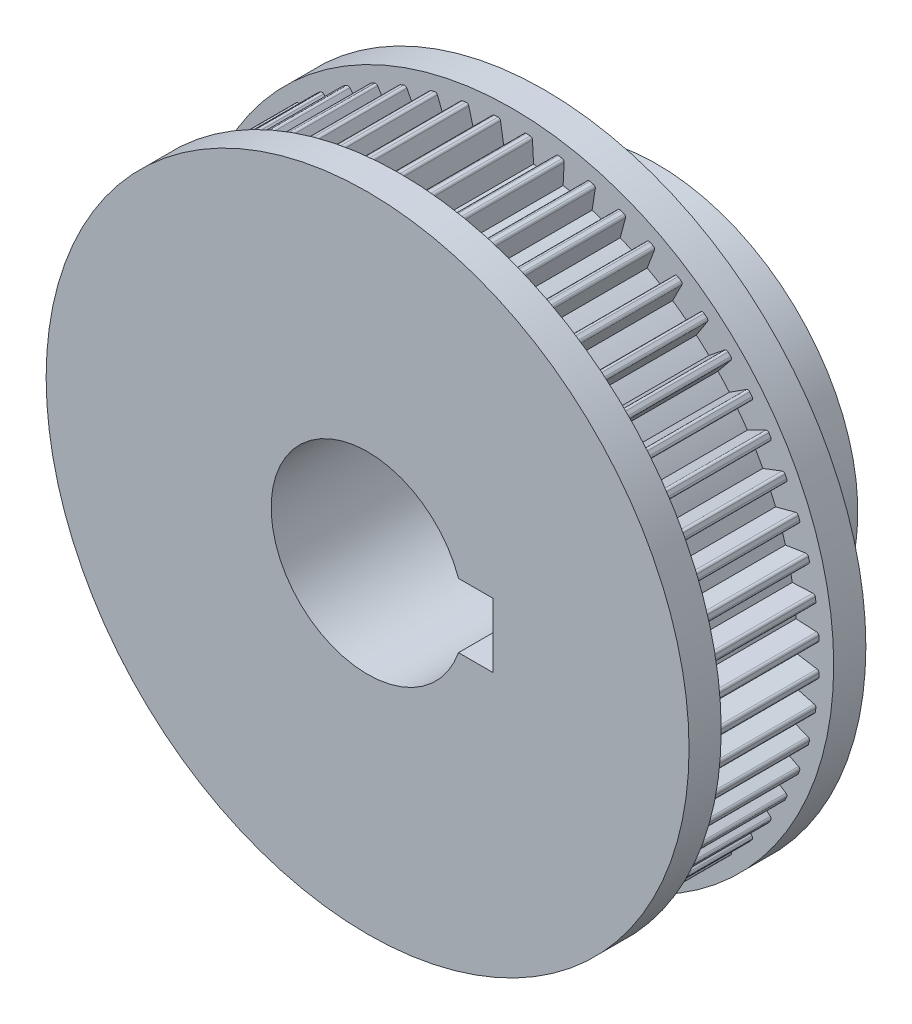
SolidWorks part; units mm, degrees
ref_plane "Front Plane" through (0, 0, 0) normal (0, 0, 1) x (1, 0, 0)
ref_plane "Top Plane" through (0, 0, 0) normal (0, 1, 0) x (1, 0, 0)
ref_plane "Right Plane" through (0, 0, 0) normal (1, 0, 0) x (0, 0, -1)
sketch "Sketch1" plane through (0, 0, 0) normal (0, 0, 1) x (1, 0, 0)
  line L0 (0, 0) -> (0, 9.7797) construction
  line L1 (0, 0) -> (0.9553, 9.0894) construction
  line L2 (-0.7503, 19.0926) -> (-0.527, 17.6995)
  line L3 (1.2496, 19.0664) -> (1.3259, 17.6576) construction
  line L4 (0.7503, 19.0926) -> (0.527, 17.6995)
  line L5 (2.7419, 18.9096) -> (2.3743, 17.5474) construction
  line L6 (1.2496, 19.0664) -> (1.3259, 17.6576)
  line L7 (2.7419, 18.9096) -> (2.3743, 17.5474)
  line L8 (3.2357, 18.8314) -> (3.1644, 17.4223)
  line L9 (4.7034, 18.5194) -> (4.1955, 17.2031)
  line L10 (5.1864, 18.39) -> (4.9682, 16.9961)
  line L11 (6.6135, 17.9263) -> (5.9707, 16.6703)
  line L12 (7.0803, 17.7471) -> (6.7175, 16.3836)
  line L13 (8.451, 17.1368) -> (7.6805, 15.9549)
  line L14 (8.8966, 16.9098) -> (8.3933, 15.5917)
  line L15 (10.196, 16.1595) -> (9.3062, 15.0647)
  line L16 (10.6154, 15.8872) -> (9.9771, 14.629)
  line L17 (11.8293, 15.0052) -> (10.8299, 14.0094)
  line L18 (12.2179, 14.6906) -> (11.4516, 13.5059)
  line L19 (13.333, 13.6865) -> (12.2349, 12.8006)
  line L20 (13.6865, 13.333) -> (12.8006, 12.2349)
  line L21 (14.6906, 12.2179) -> (13.5059, 11.4516)
  line L22 (15.0052, 11.8293) -> (14.0094, 10.8299)
  line L23 (15.8872, 10.6154) -> (14.629, 9.9771)
  line L24 (16.1595, 10.196) -> (15.0647, 9.3062)
  line L25 (16.9098, 8.8966) -> (15.5917, 8.3933)
  line L26 (17.1368, 8.451) -> (15.9549, 7.6805)
  line L27 (17.7471, 7.0803) -> (16.3836, 6.7175)
  line L28 (17.9263, 6.6135) -> (16.6703, 5.9707)
  line L29 (18.39, 5.1864) -> (16.9961, 4.9682)
  line L30 (18.5194, 4.7034) -> (17.2031, 4.1955)
  line L31 (18.8314, 3.2357) -> (17.4223, 3.1644)
  line L32 (18.9096, 2.7419) -> (17.5474, 2.3743)
  line L33 (19.0664, 1.2496) -> (17.6576, 1.3259)
  line L34 (19.0926, 0.7503) -> (17.6995, 0.527)
  line L35 (19.0926, -0.7503) -> (17.6995, -0.527)
  line L36 (19.0664, -1.2496) -> (17.6576, -1.3259)
  line L37 (18.9096, -2.7419) -> (17.5474, -2.3743)
  line L38 (18.8314, -3.2357) -> (17.4223, -3.1644)
  line L39 (18.5194, -4.7034) -> (17.2031, -4.1955)
  line L40 (18.39, -5.1864) -> (16.9961, -4.9682)
  line L41 (17.9263, -6.6135) -> (16.6703, -5.9707)
  line L42 (17.7471, -7.0803) -> (16.3836, -6.7175)
  line L43 (17.1368, -8.451) -> (15.9549, -7.6805)
  line L44 (16.9098, -8.8966) -> (15.5917, -8.3933)
  line L45 (16.1595, -10.196) -> (15.0647, -9.3062)
  line L46 (15.8872, -10.6154) -> (14.629, -9.9771)
  line L47 (15.0052, -11.8293) -> (14.0094, -10.8299)
  line L48 (14.6906, -12.2179) -> (13.5059, -11.4516)
  line L49 (13.6865, -13.333) -> (12.8006, -12.2349)
  line L50 (13.333, -13.6865) -> (12.2349, -12.8006)
  line L51 (12.2179, -14.6906) -> (11.4516, -13.5059)
  line L52 (11.8293, -15.0052) -> (10.8299, -14.0094)
  line L53 (10.6154, -15.8872) -> (9.9771, -14.629)
  line L54 (10.196, -16.1595) -> (9.3062, -15.0647)
  line L55 (8.8966, -16.9098) -> (8.3933, -15.5917)
  line L56 (8.451, -17.1368) -> (7.6805, -15.9549)
  line L57 (7.0803, -17.7471) -> (6.7175, -16.3836)
  line L58 (6.6135, -17.9263) -> (5.9707, -16.6703)
  line L59 (5.1864, -18.39) -> (4.9682, -16.9961)
  line L60 (4.7034, -18.5194) -> (4.1955, -17.2031)
  line L61 (3.2357, -18.8314) -> (3.1644, -17.4223)
  line L62 (2.7419, -18.9096) -> (2.3743, -17.5474)
  line L63 (1.2496, -19.0664) -> (1.3259, -17.6576)
  line L64 (0.7503, -19.0926) -> (0.527, -17.6995)
  line L65 (-0.7503, -19.0926) -> (-0.527, -17.6995)
  line L66 (-1.2496, -19.0664) -> (-1.3259, -17.6576)
  line L67 (-2.7419, -18.9096) -> (-2.3743, -17.5474)
  line L68 (-3.2357, -18.8314) -> (-3.1644, -17.4223)
  line L69 (-4.7034, -18.5194) -> (-4.1955, -17.2031)
  line L70 (-5.1864, -18.39) -> (-4.9682, -16.9961)
  line L71 (-6.6135, -17.9263) -> (-5.9707, -16.6703)
  line L72 (-7.0803, -17.7471) -> (-6.7175, -16.3836)
  line L73 (-8.451, -17.1368) -> (-7.6805, -15.9549)
  line L74 (-8.8966, -16.9098) -> (-8.3933, -15.5917)
  line L75 (-10.196, -16.1595) -> (-9.3062, -15.0647)
  line L76 (-10.6154, -15.8872) -> (-9.9771, -14.629)
  line L77 (-11.8293, -15.0052) -> (-10.8299, -14.0094)
  line L78 (-12.2179, -14.6906) -> (-11.4516, -13.5059)
  line L79 (-13.333, -13.6865) -> (-12.2349, -12.8006)
  line L80 (-13.6865, -13.333) -> (-12.8006, -12.2349)
  line L81 (-14.6906, -12.2179) -> (-13.5059, -11.4516)
  line L82 (-15.0052, -11.8293) -> (-14.0094, -10.8299)
  line L83 (-15.8872, -10.6154) -> (-14.629, -9.9771)
  line L84 (-16.1595, -10.196) -> (-15.0647, -9.3062)
  line L85 (-16.9098, -8.8966) -> (-15.5917, -8.3933)
  line L86 (-17.1368, -8.451) -> (-15.9549, -7.6805)
  line L87 (-17.7471, -7.0803) -> (-16.3836, -6.7175)
  line L88 (-17.9263, -6.6135) -> (-16.6703, -5.9707)
  line L89 (-18.39, -5.1864) -> (-16.9961, -4.9682)
  line L90 (-18.5194, -4.7034) -> (-17.2031, -4.1955)
  line L91 (-18.8314, -3.2357) -> (-17.4223, -3.1644)
  line L92 (-18.9096, -2.7419) -> (-17.5474, -2.3743)
  line L93 (-19.0664, -1.2496) -> (-17.6576, -1.3259)
  line L94 (-19.0926, -0.7503) -> (-17.6995, -0.527)
  line L95 (-19.0926, 0.7503) -> (-17.6995, 0.527)
  line L96 (-19.0664, 1.2496) -> (-17.6576, 1.3259)
  line L97 (-18.9096, 2.7419) -> (-17.5474, 2.3743)
  line L98 (-18.8314, 3.2357) -> (-17.4223, 3.1644)
  line L99 (-18.5194, 4.7034) -> (-17.2031, 4.1955)
  line L100 (-18.39, 5.1864) -> (-16.9961, 4.9682)
  line L101 (-17.9263, 6.6135) -> (-16.6703, 5.9707)
  line L102 (-17.7471, 7.0803) -> (-16.3836, 6.7175)
  line L103 (-17.1368, 8.451) -> (-15.9549, 7.6805)
  line L104 (-16.9098, 8.8966) -> (-15.5917, 8.3933)
  line L105 (-16.1595, 10.196) -> (-15.0647, 9.3062)
  line L106 (-15.8872, 10.6154) -> (-14.629, 9.9771)
  line L107 (-15.0052, 11.8293) -> (-14.0094, 10.8299)
  line L108 (-14.6906, 12.2179) -> (-13.5059, 11.4516)
  line L109 (-13.6865, 13.333) -> (-12.8006, 12.2349)
  line L110 (-13.333, 13.6865) -> (-12.2349, 12.8006)
  line L111 (-12.2179, 14.6906) -> (-11.4516, 13.5059)
  line L112 (-11.8293, 15.0052) -> (-10.8299, 14.0094)
  line L113 (-10.6154, 15.8872) -> (-9.9771, 14.629)
  line L114 (-10.196, 16.1595) -> (-9.3062, 15.0647)
  line L115 (-8.8966, 16.9098) -> (-8.3933, 15.5917)
  line L116 (-8.451, 17.1368) -> (-7.6805, 15.9549)
  line L117 (-7.0803, 17.7471) -> (-6.7175, 16.3836)
  line L118 (-6.6135, 17.9263) -> (-5.9707, 16.6703)
  line L119 (-5.1864, 18.39) -> (-4.9682, 16.9961)
  line L120 (-4.7034, 18.5194) -> (-4.1955, 17.2031)
  line L121 (-3.2357, 18.8314) -> (-3.1644, 17.4223)
  line L122 (-2.7419, 18.9096) -> (-2.3743, 17.5474)
  line L123 (-1.2496, 19.0664) -> (-1.3259, 17.6576)
  arc A0 (2.3743, 17.5474) -> (1.3259, 17.6576) centre (0, 0) ccw construction
  arc A1 (2.7419, 18.9096) -> (1.2496, 19.0664) centre (0, 0) ccw construction
  arc A2 (0.527, 17.6995) -> (-0.527, 17.6995) centre (0, 0) ccw
  arc A3 (0.7503, 19.0926) -> (-0.7503, 19.0926) centre (0, 0) ccw
  arc A4 (2.7419, 18.9096) -> (1.2496, 19.0664) centre (0, 0) ccw
  arc A5 (2.3743, 17.5474) -> (1.3259, 17.6576) centre (0, 0) ccw
  arc A6 (4.7034, 18.5194) -> (3.2357, 18.8314) centre (0, 0) ccw
  arc A7 (4.1955, 17.2031) -> (3.1644, 17.4223) centre (0, 0) ccw
  arc A8 (6.6135, 17.9263) -> (5.1864, 18.39) centre (0, 0) ccw
  arc A9 (5.9707, 16.6703) -> (4.9682, 16.9961) centre (0, 0) ccw
  arc A10 (8.451, 17.1368) -> (7.0803, 17.7471) centre (0, 0) ccw
  arc A11 (7.6805, 15.9549) -> (6.7175, 16.3836) centre (0, 0) ccw
  arc A12 (10.196, 16.1595) -> (8.8966, 16.9098) centre (0, 0) ccw
  arc A13 (9.3062, 15.0647) -> (8.3933, 15.5917) centre (0, 0) ccw
  arc A14 (11.8293, 15.0052) -> (10.6154, 15.8872) centre (0, 0) ccw
  arc A15 (10.8299, 14.0094) -> (9.9771, 14.629) centre (0, 0) ccw
  arc A16 (13.333, 13.6865) -> (12.2179, 14.6906) centre (0, 0) ccw
  arc A17 (12.2349, 12.8006) -> (11.4516, 13.5059) centre (0, 0) ccw
  arc A18 (14.6906, 12.2179) -> (13.6865, 13.333) centre (0, 0) ccw
  arc A19 (13.5059, 11.4516) -> (12.8006, 12.2349) centre (0, 0) ccw
  arc A20 (15.8872, 10.6154) -> (15.0052, 11.8293) centre (0, 0) ccw
  arc A21 (14.629, 9.9771) -> (14.0094, 10.8299) centre (0, 0) ccw
  arc A22 (16.9098, 8.8966) -> (16.1595, 10.196) centre (0, 0) ccw
  arc A23 (15.5917, 8.3933) -> (15.0647, 9.3062) centre (0, 0) ccw
  arc A24 (17.7471, 7.0803) -> (17.1368, 8.451) centre (0, 0) ccw
  arc A25 (16.3836, 6.7175) -> (15.9549, 7.6805) centre (0, 0) ccw
  arc A26 (18.39, 5.1864) -> (17.9263, 6.6135) centre (0, 0) ccw
  arc A27 (16.9961, 4.9682) -> (16.6703, 5.9707) centre (0, 0) ccw
  arc A28 (18.8314, 3.2357) -> (18.5194, 4.7034) centre (0, 0) ccw
  arc A29 (17.4223, 3.1644) -> (17.2031, 4.1955) centre (0, 0) ccw
  arc A30 (19.0664, 1.2496) -> (18.9096, 2.7419) centre (0, 0) ccw
  arc A31 (17.6576, 1.3259) -> (17.5474, 2.3743) centre (0, 0) ccw
  arc A32 (19.0926, -0.7503) -> (19.0926, 0.7503) centre (0, 0) ccw
  arc A33 (17.6995, -0.527) -> (17.6995, 0.527) centre (0, 0) ccw
  arc A34 (18.9096, -2.7419) -> (19.0664, -1.2496) centre (0, 0) ccw
  arc A35 (17.5474, -2.3743) -> (17.6576, -1.3259) centre (0, 0) ccw
  arc A36 (18.5194, -4.7034) -> (18.8314, -3.2357) centre (0, 0) ccw
  arc A37 (17.2031, -4.1955) -> (17.4223, -3.1644) centre (0, 0) ccw
  arc A38 (17.9263, -6.6135) -> (18.39, -5.1864) centre (0, 0) ccw
  arc A39 (16.6703, -5.9707) -> (16.9961, -4.9682) centre (0, 0) ccw
  arc A40 (17.1368, -8.451) -> (17.7471, -7.0803) centre (0, 0) ccw
  arc A41 (15.9549, -7.6805) -> (16.3836, -6.7175) centre (0, 0) ccw
  arc A42 (16.1595, -10.196) -> (16.9098, -8.8966) centre (0, 0) ccw
  arc A43 (15.0647, -9.3062) -> (15.5917, -8.3933) centre (0, 0) ccw
  arc A44 (15.0052, -11.8293) -> (15.8872, -10.6154) centre (0, 0) ccw
  arc A45 (14.0094, -10.8299) -> (14.629, -9.9771) centre (0, 0) ccw
  arc A46 (13.6865, -13.333) -> (14.6906, -12.2179) centre (0, 0) ccw
  arc A47 (12.8006, -12.2349) -> (13.5059, -11.4516) centre (0, 0) ccw
  arc A48 (12.2179, -14.6906) -> (13.333, -13.6865) centre (0, 0) ccw
  arc A49 (11.4516, -13.5059) -> (12.2349, -12.8006) centre (0, 0) ccw
  arc A50 (10.6154, -15.8872) -> (11.8293, -15.0052) centre (0, 0) ccw
  arc A51 (9.9771, -14.629) -> (10.8299, -14.0094) centre (0, 0) ccw
  arc A52 (8.8966, -16.9098) -> (10.196, -16.1595) centre (0, 0) ccw
  arc A53 (8.3933, -15.5917) -> (9.3062, -15.0647) centre (0, 0) ccw
  arc A54 (7.0803, -17.7471) -> (8.451, -17.1368) centre (0, 0) ccw
  arc A55 (6.7175, -16.3836) -> (7.6805, -15.9549) centre (0, 0) ccw
  arc A56 (5.1864, -18.39) -> (6.6135, -17.9263) centre (0, 0) ccw
  arc A57 (4.9682, -16.9961) -> (5.9707, -16.6703) centre (0, 0) ccw
  arc A58 (3.2357, -18.8314) -> (4.7034, -18.5194) centre (0, 0) ccw
  arc A59 (3.1644, -17.4223) -> (4.1955, -17.2031) centre (0, 0) ccw
  arc A60 (1.2496, -19.0664) -> (2.7419, -18.9096) centre (0, 0) ccw
  arc A61 (1.3259, -17.6576) -> (2.3743, -17.5474) centre (0, 0) ccw
  arc A62 (-0.7503, -19.0926) -> (0.7503, -19.0926) centre (0, 0) ccw
  arc A63 (-0.527, -17.6995) -> (0.527, -17.6995) centre (0, 0) ccw
  arc A64 (-2.7419, -18.9096) -> (-1.2496, -19.0664) centre (0, 0) ccw
  arc A65 (-2.3743, -17.5474) -> (-1.3259, -17.6576) centre (0, 0) ccw
  arc A66 (-4.7034, -18.5194) -> (-3.2357, -18.8314) centre (0, 0) ccw
  arc A67 (-4.1955, -17.2031) -> (-3.1644, -17.4223) centre (0, 0) ccw
  arc A68 (-6.6135, -17.9263) -> (-5.1864, -18.39) centre (0, 0) ccw
  arc A69 (-5.9707, -16.6703) -> (-4.9682, -16.9961) centre (0, 0) ccw
  arc A70 (-8.451, -17.1368) -> (-7.0803, -17.7471) centre (0, 0) ccw
  arc A71 (-7.6805, -15.9549) -> (-6.7175, -16.3836) centre (0, 0) ccw
  arc A72 (-10.196, -16.1595) -> (-8.8966, -16.9098) centre (0, 0) ccw
  arc A73 (-9.3062, -15.0647) -> (-8.3933, -15.5917) centre (0, 0) ccw
  arc A74 (-11.8293, -15.0052) -> (-10.6154, -15.8872) centre (0, 0) ccw
  arc A75 (-10.8299, -14.0094) -> (-9.9771, -14.629) centre (0, 0) ccw
  arc A76 (-13.333, -13.6865) -> (-12.2179, -14.6906) centre (0, 0) ccw
  arc A77 (-12.2349, -12.8006) -> (-11.4516, -13.5059) centre (0, 0) ccw
  arc A78 (-14.6906, -12.2179) -> (-13.6865, -13.333) centre (0, 0) ccw
  arc A79 (-13.5059, -11.4516) -> (-12.8006, -12.2349) centre (0, 0) ccw
  arc A80 (-15.8872, -10.6154) -> (-15.0052, -11.8293) centre (0, 0) ccw
  arc A81 (-14.629, -9.9771) -> (-14.0094, -10.8299) centre (0, 0) ccw
  arc A82 (-16.9098, -8.8966) -> (-16.1595, -10.196) centre (0, 0) ccw
  arc A83 (-15.5917, -8.3933) -> (-15.0647, -9.3062) centre (0, 0) ccw
  arc A84 (-17.7471, -7.0803) -> (-17.1368, -8.451) centre (0, 0) ccw
  arc A85 (-16.3836, -6.7175) -> (-15.9549, -7.6805) centre (0, 0) ccw
  arc A86 (-18.39, -5.1864) -> (-17.9263, -6.6135) centre (0, 0) ccw
  arc A87 (-16.9961, -4.9682) -> (-16.6703, -5.9707) centre (0, 0) ccw
  arc A88 (-18.8314, -3.2357) -> (-18.5194, -4.7034) centre (0, 0) ccw
  arc A89 (-17.4223, -3.1644) -> (-17.2031, -4.1955) centre (0, 0) ccw
  arc A90 (-19.0664, -1.2496) -> (-18.9096, -2.7419) centre (0, 0) ccw
  arc A91 (-17.6576, -1.3259) -> (-17.5474, -2.3743) centre (0, 0) ccw
  arc A92 (-19.0926, 0.7503) -> (-19.0926, -0.7503) centre (0, 0) ccw
  arc A93 (-17.6995, 0.527) -> (-17.6995, -0.527) centre (0, 0) ccw
  arc A94 (-18.9096, 2.7419) -> (-19.0664, 1.2496) centre (0, 0) ccw
  arc A95 (-17.5474, 2.3743) -> (-17.6576, 1.3259) centre (0, 0) ccw
  arc A96 (-18.5194, 4.7034) -> (-18.8314, 3.2357) centre (0, 0) ccw
  arc A97 (-17.2031, 4.1955) -> (-17.4223, 3.1644) centre (0, 0) ccw
  arc A98 (-17.9263, 6.6135) -> (-18.39, 5.1864) centre (0, 0) ccw
  arc A99 (-16.6703, 5.9707) -> (-16.9961, 4.9682) centre (0, 0) ccw
  arc A100 (-17.1368, 8.451) -> (-17.7471, 7.0803) centre (0, 0) ccw
  arc A101 (-15.9549, 7.6805) -> (-16.3836, 6.7175) centre (0, 0) ccw
  arc A102 (-16.1595, 10.196) -> (-16.9098, 8.8966) centre (0, 0) ccw
  arc A103 (-15.0647, 9.3062) -> (-15.5917, 8.3933) centre (0, 0) ccw
  arc A104 (-15.0052, 11.8293) -> (-15.8872, 10.6154) centre (0, 0) ccw
  arc A105 (-14.0094, 10.8299) -> (-14.629, 9.9771) centre (0, 0) ccw
  arc A106 (-13.6865, 13.333) -> (-14.6906, 12.2179) centre (0, 0) ccw
  arc A107 (-12.8006, 12.2349) -> (-13.5059, 11.4516) centre (0, 0) ccw
  arc A108 (-12.2179, 14.6906) -> (-13.333, 13.6865) centre (0, 0) ccw
  arc A109 (-11.4516, 13.5059) -> (-12.2349, 12.8006) centre (0, 0) ccw
  arc A110 (-10.6154, 15.8872) -> (-11.8293, 15.0052) centre (0, 0) ccw
  arc A111 (-9.9771, 14.629) -> (-10.8299, 14.0094) centre (0, 0) ccw
  arc A112 (-8.8966, 16.9098) -> (-10.196, 16.1595) centre (0, 0) ccw
  arc A113 (-8.3933, 15.5917) -> (-9.3062, 15.0647) centre (0, 0) ccw
  arc A114 (-7.0803, 17.7471) -> (-8.451, 17.1368) centre (0, 0) ccw
  arc A115 (-6.7175, 16.3836) -> (-7.6805, 15.9549) centre (0, 0) ccw
  arc A116 (-5.1864, 18.39) -> (-6.6135, 17.9263) centre (0, 0) ccw
  arc A117 (-4.9682, 16.9961) -> (-5.9707, 16.6703) centre (0, 0) ccw
  arc A118 (-3.2357, 18.8314) -> (-4.7034, 18.5194) centre (0, 0) ccw
  arc A119 (-3.1644, 17.4223) -> (-4.1955, 17.2031) centre (0, 0) ccw
  arc A120 (-1.2496, 19.0664) -> (-2.7419, 18.9096) centre (0, 0) ccw
  arc A121 (-1.3259, 17.6576) -> (-2.3743, 17.5474) centre (0, 0) ccw
  point P1 (0, 19.1073)
  point P2 (1.9973, 19.0027)
  point P253 (0, 0)
  dimension "D1" = 1.4
  dimension "D2" = 0.8
  dimension "D3" = 0.5
  dimension "D4" = 2
  dimension "D5" = 60
sketch "Sketch2" plane through (0, 0, 0) normal (0, 0, 1) x (1, 0, 0)
  circle A0 centre (0, 0) radius 19.1073
extrude "Boss-Extrude1" add sketch "Sketch2" along normal blind 7
extrude "Cut-Extrude1" cut sketch "Sketch1" along normal blind 22
fillet "Fillet1" radius 0.15 4 edges at (-8.3933, 15.5917, 3.5) (-8.8966, 16.9098, 3.5) (-7.6805, 15.9549, 3.5) (-8.451, 17.1368, 3.5)
sketch "Sketch3" plane through (0, 0, 0) normal (0, 0, -1) x (-1, 0, 0)
  circle A0 centre (0, 0) radius 8
  dimension "D1" = 16
extrude "Cut-Extrude2" cut sketch "Sketch3" against normal blind 22
sketch "Sketch5" plane through (0, 0, 7) normal (0, 0, 1) x (1, 0, 0)
  line L0 (-0.527, 17.6995) -> (-0.7503, 19.0926) construction
  line L1 (-1.2496, 19.0664) -> (-1.3259, 17.6576) construction
  line L2 (0.7503, 19.0926) -> (0.7291, 18.9607)
  line L3 (1.2568, 18.9331) -> (1.2496, 19.0664)
  line L4 (-0.7291, 18.9607) -> (-0.7503, 19.0926)
  line L5 (-1.2496, 19.0664) -> (-1.2568, 18.9331)
  line L6 (2.7419, 18.9096) -> (2.7071, 18.7807)
  line L7 (3.229, 18.698) -> (3.2357, 18.8314)
  line L8 (4.7034, 18.5194) -> (4.6554, 18.3948)
  line L9 (5.1657, 18.2581) -> (5.1864, 18.39)
  line L10 (6.6135, 17.9263) -> (6.5526, 17.8074)
  line L11 (7.0459, 17.6181) -> (7.0803, 17.7471)
  line L12 (8.451, 17.1368) -> (8.3781, 17.0249)
  line L13 (8.8489, 16.7851) -> (8.8966, 16.9098)
  line L14 (10.196, 16.1595) -> (10.1118, 16.0559)
  line L15 (10.555, 15.7681) -> (10.6154, 15.8872)
  line L16 (11.8293, 15.0052) -> (11.7347, 14.911)
  line L17 (12.1454, 14.5785) -> (12.2179, 14.6906)
  line L18 (13.333, 13.6865) -> (13.2291, 13.6027)
  line L19 (13.6027, 13.2291) -> (13.6865, 13.333)
  line L20 (14.6906, 12.2179) -> (14.5785, 12.1454)
  line L21 (14.911, 11.7347) -> (15.0052, 11.8293)
  line L22 (15.8872, 10.6154) -> (15.7681, 10.555)
  line L23 (16.0559, 10.1118) -> (16.1595, 10.196)
  line L24 (16.9098, 8.8966) -> (16.7851, 8.8489)
  line L25 (17.0249, 8.3781) -> (17.1368, 8.451)
  line L26 (17.7471, 7.0803) -> (17.6181, 7.0459)
  line L27 (17.8074, 6.5526) -> (17.9263, 6.6135)
  line L28 (18.39, 5.1864) -> (18.2581, 5.1657)
  line L29 (18.3948, 4.6554) -> (18.5194, 4.7034)
  line L30 (18.8314, 3.2357) -> (18.698, 3.229)
  line L31 (18.7807, 2.7071) -> (18.9096, 2.7419)
  line L32 (19.0664, 1.2496) -> (18.9331, 1.2568)
  line L33 (18.9607, 0.7291) -> (19.0926, 0.7503)
  line L34 (19.0926, -0.7503) -> (18.9607, -0.7291)
  line L35 (18.9331, -1.2568) -> (19.0664, -1.2496)
  line L36 (18.9096, -2.7419) -> (18.7807, -2.7071)
  line L37 (18.698, -3.229) -> (18.8314, -3.2357)
  line L38 (18.5194, -4.7034) -> (18.3948, -4.6554)
  line L39 (18.2581, -5.1657) -> (18.39, -5.1864)
  line L40 (17.9263, -6.6135) -> (17.8074, -6.5526)
  line L41 (17.6181, -7.0459) -> (17.7471, -7.0803)
  line L42 (17.1368, -8.451) -> (17.0249, -8.3781)
  line L43 (16.7851, -8.8489) -> (16.9098, -8.8966)
  line L44 (16.1595, -10.196) -> (16.0559, -10.1118)
  line L45 (15.7681, -10.555) -> (15.8872, -10.6154)
  line L46 (15.0052, -11.8293) -> (14.911, -11.7347)
  line L47 (14.5785, -12.1454) -> (14.6906, -12.2179)
  line L48 (13.6865, -13.333) -> (13.6027, -13.2291)
  line L49 (13.2291, -13.6027) -> (13.333, -13.6865)
  line L50 (12.2179, -14.6906) -> (12.1454, -14.5785)
  line L51 (11.7347, -14.911) -> (11.8293, -15.0052)
  line L52 (10.6154, -15.8872) -> (10.555, -15.7681)
  line L53 (10.1118, -16.0559) -> (10.196, -16.1595)
  line L54 (8.8966, -16.9098) -> (8.8489, -16.7851)
  line L55 (8.3781, -17.0249) -> (8.451, -17.1368)
  line L56 (7.0803, -17.7471) -> (7.0459, -17.6181)
  line L57 (6.5526, -17.8074) -> (6.6135, -17.9263)
  line L58 (5.1864, -18.39) -> (5.1657, -18.2581)
  line L59 (4.6554, -18.3948) -> (4.7034, -18.5194)
  line L60 (3.2357, -18.8314) -> (3.229, -18.698)
  line L61 (2.7071, -18.7807) -> (2.7419, -18.9096)
  line L62 (1.2496, -19.0664) -> (1.2568, -18.9331)
  line L63 (0.7291, -18.9607) -> (0.7503, -19.0926)
  line L64 (-0.7503, -19.0926) -> (-0.7291, -18.9607)
  line L65 (-1.2568, -18.9331) -> (-1.2496, -19.0664)
  line L66 (-2.7419, -18.9096) -> (-2.7071, -18.7807)
  line L67 (-3.229, -18.698) -> (-3.2357, -18.8314)
  line L68 (-4.7034, -18.5194) -> (-4.6554, -18.3948)
  line L69 (-5.1657, -18.2581) -> (-5.1864, -18.39)
  line L70 (-6.6135, -17.9263) -> (-6.5526, -17.8074)
  line L71 (-7.0459, -17.6181) -> (-7.0803, -17.7471)
  line L72 (-8.451, -17.1368) -> (-8.3781, -17.0249)
  line L73 (-8.8489, -16.7851) -> (-8.8966, -16.9098)
  line L74 (-10.196, -16.1595) -> (-10.1118, -16.0559)
  line L75 (-10.555, -15.7681) -> (-10.6154, -15.8872)
  line L76 (-11.8293, -15.0052) -> (-11.7347, -14.911)
  line L77 (-12.1454, -14.5785) -> (-12.2179, -14.6906)
  line L78 (-13.333, -13.6865) -> (-13.2291, -13.6027)
  line L79 (-13.6027, -13.2291) -> (-13.6865, -13.333)
  line L80 (-14.6906, -12.2179) -> (-14.5785, -12.1454)
  line L81 (-14.911, -11.7347) -> (-15.0052, -11.8293)
  line L82 (-15.8872, -10.6154) -> (-15.7681, -10.555)
  line L83 (-16.0559, -10.1118) -> (-16.1595, -10.196)
  line L84 (-16.9098, -8.8966) -> (-16.7851, -8.8489)
  line L85 (-17.0249, -8.3781) -> (-17.1368, -8.451)
  line L86 (-17.7471, -7.0803) -> (-17.6181, -7.0459)
  line L87 (-17.8074, -6.5526) -> (-17.9263, -6.6135)
  line L88 (-18.39, -5.1864) -> (-18.2581, -5.1657)
  line L89 (-18.3948, -4.6554) -> (-18.5194, -4.7034)
  line L90 (-18.8314, -3.2357) -> (-18.698, -3.229)
  line L91 (-18.7807, -2.7071) -> (-18.9096, -2.7419)
  line L92 (-19.0664, -1.2496) -> (-18.9331, -1.2568)
  line L93 (-18.9607, -0.7291) -> (-19.0926, -0.7503)
  line L94 (-19.0926, 0.7503) -> (-18.9607, 0.7291)
  line L95 (-18.9331, 1.2568) -> (-19.0664, 1.2496)
  line L96 (-18.9096, 2.7419) -> (-18.7807, 2.7071)
  line L97 (-18.698, 3.229) -> (-18.8314, 3.2357)
  line L98 (-18.5194, 4.7034) -> (-18.3948, 4.6554)
  line L99 (-18.2581, 5.1657) -> (-18.39, 5.1864)
  line L100 (-17.9263, 6.6135) -> (-17.8074, 6.5526)
  line L101 (-17.6181, 7.0459) -> (-17.7471, 7.0803)
  line L102 (-17.1368, 8.451) -> (-17.0249, 8.3781)
  line L103 (-16.7851, 8.8489) -> (-16.9098, 8.8966)
  line L104 (-16.1595, 10.196) -> (-16.0559, 10.1118)
  line L105 (-15.7681, 10.555) -> (-15.8872, 10.6154)
  line L106 (-15.0052, 11.8293) -> (-14.911, 11.7347)
  line L107 (-14.5785, 12.1454) -> (-14.6906, 12.2179)
  line L108 (-13.6865, 13.333) -> (-13.6027, 13.2291)
  line L109 (-13.2291, 13.6027) -> (-13.333, 13.6865)
  line L110 (-12.2179, 14.6906) -> (-12.1454, 14.5785)
  line L111 (-11.7347, 14.911) -> (-11.8293, 15.0052)
  line L112 (-10.6154, 15.8872) -> (-10.555, 15.7681)
  line L113 (-10.1118, 16.0559) -> (-10.196, 16.1595)
  line L114 (-8.8966, 16.9098) -> (-8.8489, 16.7851)
  line L115 (-8.3781, 17.0249) -> (-8.451, 17.1368)
  line L116 (-7.0803, 17.7471) -> (-7.0459, 17.6181)
  line L117 (-6.5526, 17.8074) -> (-6.6135, 17.9263)
  line L118 (-5.1864, 18.39) -> (-5.1657, 18.2581)
  line L119 (-4.6554, 18.3948) -> (-4.7034, 18.5194)
  line L120 (-3.2357, 18.8314) -> (-3.229, 18.698)
  line L121 (-2.7071, 18.7807) -> (-2.7419, 18.9096)
  arc A0 (-0.7503, 19.0926) -> (-1.2496, 19.0664) centre (0, 0) ccw construction
  arc A2 (-0.8842, 19.0869) -> (-0.7291, 18.9607) centre (-0.8772, 18.937) cw
  arc A3 (-1.1158, 19.0747) -> (-1.2568, 18.9331) centre (-1.107, 18.925) ccw
  arc A4 (-0.7503, 19.0926) -> (-0.8842, 19.0869) centre (0, 0) ccw
  arc A5 (-1.1158, 19.0747) -> (-1.2496, 19.0664) centre (0, 0) ccw
  arc A6 (0.8842, 19.0869) -> (0.7291, 18.9607) centre (0.8772, 18.937) ccw
  arc A7 (0.8842, 19.0869) -> (0.7503, 19.0926) centre (0, 0) ccw
  arc A8 (1.1158, 19.0747) -> (1.2568, 18.9331) centre (1.107, 18.925) cw
  arc A9 (1.2496, 19.0664) -> (1.1158, 19.0747) centre (0, 0) ccw
  arc A10 (2.8745, 18.8899) -> (2.7071, 18.7807) centre (2.8519, 18.7416) ccw
  arc A11 (2.8745, 18.8899) -> (2.7419, 18.9096) centre (0, 0) ccw
  arc A12 (3.1035, 18.8536) -> (3.229, 18.698) centre (3.0792, 18.7056) cw
  arc A13 (3.2357, 18.8314) -> (3.1035, 18.8536) centre (0, 0) ccw
  arc A14 (4.8332, 18.4859) -> (4.6554, 18.3948) centre (4.7953, 18.3408) ccw
  arc A15 (4.8332, 18.4859) -> (4.7034, 18.5194) centre (0, 0) ccw
  arc A16 (5.0573, 18.4259) -> (5.1657, 18.2581) centre (5.0176, 18.2813) cw
  arc A17 (5.1864, 18.39) -> (5.0573, 18.4259) centre (0, 0) ccw
  arc A18 (6.7391, 17.8794) -> (6.5526, 17.8074) centre (6.6862, 17.7391) ccw
  arc A19 (6.7391, 17.8794) -> (6.6135, 17.9263) centre (0, 0) ccw
  arc A20 (6.9556, 17.7963) -> (7.0459, 17.6181) centre (6.901, 17.6566) cw
  arc A21 (7.0803, 17.7471) -> (6.9556, 17.7963) centre (0, 0) ccw
  arc A22 (8.5711, 17.0771) -> (8.3781, 17.0249) centre (8.5038, 16.943) ccw
  arc A23 (8.5711, 17.0771) -> (8.451, 17.1368) centre (0, 0) ccw
  arc A24 (8.7777, 16.9718) -> (8.8489, 16.7851) centre (8.7088, 16.8386) cw
  arc A25 (8.8966, 16.9098) -> (8.7777, 16.9718) centre (0, 0) ccw
  arc A26 (10.3092, 16.0876) -> (10.1118, 16.0559) centre (10.2282, 15.9613) ccw
  arc A27 (10.3092, 16.0876) -> (10.196, 16.1595) centre (0, 0) ccw
  arc A28 (10.5037, 15.9613) -> (10.555, 15.7681) centre (10.4212, 15.836) cw
  arc A29 (10.6154, 15.8872) -> (10.5037, 15.9613) centre (0, 0) ccw
  arc A30 (11.9343, 14.9219) -> (11.7347, 14.911) centre (11.8406, 14.8047) ccw
  arc A31 (11.9343, 14.9219) -> (11.8293, 15.0052) centre (0, 0) ccw
  arc A32 (12.1145, 14.7759) -> (12.1454, 14.5785) centre (12.0194, 14.6599) cw
  arc A33 (12.2179, 14.6906) -> (12.1145, 14.7759) centre (0, 0) ccw
  arc A34 (13.4287, 13.5927) -> (13.2291, 13.6027) centre (13.3233, 13.486) ccw
  arc A35 (13.4287, 13.5927) -> (13.333, 13.6865) centre (0, 0) ccw
  arc A36 (13.5927, 13.4287) -> (13.6027, 13.2291) centre (13.486, 13.3233) cw
  arc A37 (13.6865, 13.333) -> (13.5927, 13.4287) centre (0, 0) ccw
  arc A38 (14.7759, 12.1145) -> (14.5785, 12.1454) centre (14.6599, 12.0194) ccw
  arc A39 (14.7759, 12.1145) -> (14.6906, 12.2179) centre (0, 0) ccw
  arc A40 (14.9219, 11.9343) -> (14.911, 11.7347) centre (14.8047, 11.8406) cw
  arc A41 (15.0052, 11.8293) -> (14.9219, 11.9343) centre (0, 0) ccw
  arc A42 (15.9613, 10.5037) -> (15.7681, 10.555) centre (15.836, 10.4212) ccw
  arc A43 (15.9613, 10.5037) -> (15.8872, 10.6154) centre (0, 0) ccw
  arc A44 (16.0876, 10.3092) -> (16.0559, 10.1118) centre (15.9613, 10.2282) cw
  arc A45 (16.1595, 10.196) -> (16.0876, 10.3092) centre (0, 0) ccw
  arc A46 (16.9718, 8.7777) -> (16.7851, 8.8489) centre (16.8386, 8.7088) ccw
  arc A47 (16.9718, 8.7777) -> (16.9098, 8.8966) centre (0, 0) ccw
  arc A48 (17.0771, 8.5711) -> (17.0249, 8.3781) centre (16.943, 8.5038) cw
  arc A49 (17.1368, 8.451) -> (17.0771, 8.5711) centre (0, 0) ccw
  arc A50 (17.7963, 6.9556) -> (17.6181, 7.0459) centre (17.6566, 6.901) ccw
  arc A51 (17.7963, 6.9556) -> (17.7471, 7.0803) centre (0, 0) ccw
  arc A52 (17.8794, 6.7391) -> (17.8074, 6.5526) centre (17.7391, 6.6862) cw
  arc A53 (17.9263, 6.6135) -> (17.8794, 6.7391) centre (0, 0) ccw
  arc A54 (18.4259, 5.0573) -> (18.2581, 5.1657) centre (18.2813, 5.0176) ccw
  arc A55 (18.4259, 5.0573) -> (18.39, 5.1864) centre (0, 0) ccw
  arc A56 (18.4859, 4.8332) -> (18.3948, 4.6554) centre (18.3408, 4.7953) cw
  arc A57 (18.5194, 4.7034) -> (18.4859, 4.8332) centre (0, 0) ccw
  arc A58 (18.8536, 3.1035) -> (18.698, 3.229) centre (18.7056, 3.0792) ccw
  arc A59 (18.8536, 3.1035) -> (18.8314, 3.2357) centre (0, 0) ccw
  arc A60 (18.8899, 2.8745) -> (18.7807, 2.7071) centre (18.7416, 2.8519) cw
  arc A61 (18.9096, 2.7419) -> (18.8899, 2.8745) centre (0, 0) ccw
  arc A62 (19.0747, 1.1158) -> (18.9331, 1.2568) centre (18.925, 1.107) ccw
  arc A63 (19.0747, 1.1158) -> (19.0664, 1.2496) centre (0, 0) ccw
  arc A64 (19.0869, 0.8842) -> (18.9607, 0.7291) centre (18.937, 0.8772) cw
  arc A65 (19.0926, 0.7503) -> (19.0869, 0.8842) centre (0, 0) ccw
  arc A66 (19.0869, -0.8842) -> (18.9607, -0.7291) centre (18.937, -0.8772) ccw
  arc A67 (19.0869, -0.8842) -> (19.0926, -0.7503) centre (0, 0) ccw
  arc A68 (19.0747, -1.1158) -> (18.9331, -1.2568) centre (18.925, -1.107) cw
  arc A69 (19.0664, -1.2496) -> (19.0747, -1.1158) centre (0, 0) ccw
  arc A70 (18.8899, -2.8745) -> (18.7807, -2.7071) centre (18.7416, -2.8519) ccw
  arc A71 (18.8899, -2.8745) -> (18.9096, -2.7419) centre (0, 0) ccw
  arc A72 (18.8536, -3.1035) -> (18.698, -3.229) centre (18.7056, -3.0792) cw
  arc A73 (18.8314, -3.2357) -> (18.8536, -3.1035) centre (0, 0) ccw
  arc A74 (18.4859, -4.8332) -> (18.3948, -4.6554) centre (18.3408, -4.7953) ccw
  arc A75 (18.4859, -4.8332) -> (18.5194, -4.7034) centre (0, 0) ccw
  arc A76 (18.4259, -5.0573) -> (18.2581, -5.1657) centre (18.2813, -5.0176) cw
  arc A77 (18.39, -5.1864) -> (18.4259, -5.0573) centre (0, 0) ccw
  arc A78 (17.8794, -6.7391) -> (17.8074, -6.5526) centre (17.7391, -6.6862) ccw
  arc A79 (17.8794, -6.7391) -> (17.9263, -6.6135) centre (0, 0) ccw
  arc A80 (17.7963, -6.9556) -> (17.6181, -7.0459) centre (17.6566, -6.901) cw
  arc A81 (17.7471, -7.0803) -> (17.7963, -6.9556) centre (0, 0) ccw
  arc A82 (17.0771, -8.5711) -> (17.0249, -8.3781) centre (16.943, -8.5038) ccw
  arc A83 (17.0771, -8.5711) -> (17.1368, -8.451) centre (0, 0) ccw
  arc A84 (16.9718, -8.7777) -> (16.7851, -8.8489) centre (16.8386, -8.7088) cw
  arc A85 (16.9098, -8.8966) -> (16.9718, -8.7777) centre (0, 0) ccw
  arc A86 (16.0876, -10.3092) -> (16.0559, -10.1118) centre (15.9613, -10.2282) ccw
  arc A87 (16.0876, -10.3092) -> (16.1595, -10.196) centre (0, 0) ccw
  arc A88 (15.9613, -10.5037) -> (15.7681, -10.555) centre (15.836, -10.4212) cw
  arc A89 (15.8872, -10.6154) -> (15.9613, -10.5037) centre (0, 0) ccw
  arc A90 (14.9219, -11.9343) -> (14.911, -11.7347) centre (14.8047, -11.8406) ccw
  arc A91 (14.9219, -11.9343) -> (15.0052, -11.8293) centre (0, 0) ccw
  arc A92 (14.7759, -12.1145) -> (14.5785, -12.1454) centre (14.6599, -12.0194) cw
  arc A93 (14.6906, -12.2179) -> (14.7759, -12.1145) centre (0, 0) ccw
  arc A94 (13.5927, -13.4287) -> (13.6027, -13.2291) centre (13.486, -13.3233) ccw
  arc A95 (13.5927, -13.4287) -> (13.6865, -13.333) centre (0, 0) ccw
  arc A96 (13.4287, -13.5927) -> (13.2291, -13.6027) centre (13.3233, -13.486) cw
  arc A97 (13.333, -13.6865) -> (13.4287, -13.5927) centre (0, 0) ccw
  arc A98 (12.1145, -14.7759) -> (12.1454, -14.5785) centre (12.0194, -14.6599) ccw
  arc A99 (12.1145, -14.7759) -> (12.2179, -14.6906) centre (0, 0) ccw
  arc A100 (11.9343, -14.9219) -> (11.7347, -14.911) centre (11.8406, -14.8047) cw
  arc A101 (11.8293, -15.0052) -> (11.9343, -14.9219) centre (0, 0) ccw
  arc A102 (10.5037, -15.9613) -> (10.555, -15.7681) centre (10.4212, -15.836) ccw
  arc A103 (10.5037, -15.9613) -> (10.6154, -15.8872) centre (0, 0) ccw
  arc A104 (10.3092, -16.0876) -> (10.1118, -16.0559) centre (10.2282, -15.9613) cw
  arc A105 (10.196, -16.1595) -> (10.3092, -16.0876) centre (0, 0) ccw
  arc A106 (8.7777, -16.9718) -> (8.8489, -16.7851) centre (8.7088, -16.8386) ccw
  arc A107 (8.7777, -16.9718) -> (8.8966, -16.9098) centre (0, 0) ccw
  arc A108 (8.5711, -17.0771) -> (8.3781, -17.0249) centre (8.5038, -16.943) cw
  arc A109 (8.451, -17.1368) -> (8.5711, -17.0771) centre (0, 0) ccw
  arc A110 (6.9556, -17.7963) -> (7.0459, -17.6181) centre (6.901, -17.6566) ccw
  arc A111 (6.9556, -17.7963) -> (7.0803, -17.7471) centre (0, 0) ccw
  arc A112 (6.7391, -17.8794) -> (6.5526, -17.8074) centre (6.6862, -17.7391) cw
  arc A113 (6.6135, -17.9263) -> (6.7391, -17.8794) centre (0, 0) ccw
  arc A114 (5.0573, -18.4259) -> (5.1657, -18.2581) centre (5.0176, -18.2813) ccw
  arc A115 (5.0573, -18.4259) -> (5.1864, -18.39) centre (0, 0) ccw
  arc A116 (4.8332, -18.4859) -> (4.6554, -18.3948) centre (4.7953, -18.3408) cw
  arc A117 (4.7034, -18.5194) -> (4.8332, -18.4859) centre (0, 0) ccw
  arc A118 (3.1035, -18.8536) -> (3.229, -18.698) centre (3.0792, -18.7056) ccw
  arc A119 (3.1035, -18.8536) -> (3.2357, -18.8314) centre (0, 0) ccw
  arc A120 (2.8745, -18.8899) -> (2.7071, -18.7807) centre (2.8519, -18.7416) cw
  arc A121 (2.7419, -18.9096) -> (2.8745, -18.8899) centre (0, 0) ccw
  arc A122 (1.1158, -19.0747) -> (1.2568, -18.9331) centre (1.107, -18.925) ccw
  arc A123 (1.1158, -19.0747) -> (1.2496, -19.0664) centre (0, 0) ccw
  arc A124 (0.8842, -19.0869) -> (0.7291, -18.9607) centre (0.8772, -18.937) cw
  arc A125 (0.7503, -19.0926) -> (0.8842, -19.0869) centre (0, 0) ccw
  arc A126 (-0.8842, -19.0869) -> (-0.7291, -18.9607) centre (-0.8772, -18.937) ccw
  arc A127 (-0.8842, -19.0869) -> (-0.7503, -19.0926) centre (0, 0) ccw
  arc A128 (-1.1158, -19.0747) -> (-1.2568, -18.9331) centre (-1.107, -18.925) cw
  arc A129 (-1.2496, -19.0664) -> (-1.1158, -19.0747) centre (0, 0) ccw
  arc A130 (-2.8745, -18.8899) -> (-2.7071, -18.7807) centre (-2.8519, -18.7416) ccw
  arc A131 (-2.8745, -18.8899) -> (-2.7419, -18.9096) centre (0, 0) ccw
  arc A132 (-3.1035, -18.8536) -> (-3.229, -18.698) centre (-3.0792, -18.7056) cw
  arc A133 (-3.2357, -18.8314) -> (-3.1035, -18.8536) centre (0, 0) ccw
  arc A134 (-4.8332, -18.4859) -> (-4.6554, -18.3948) centre (-4.7953, -18.3408) ccw
  arc A135 (-4.8332, -18.4859) -> (-4.7034, -18.5194) centre (0, 0) ccw
  arc A136 (-5.0573, -18.4259) -> (-5.1657, -18.2581) centre (-5.0176, -18.2813) cw
  arc A137 (-5.1864, -18.39) -> (-5.0573, -18.4259) centre (0, 0) ccw
  arc A138 (-6.7391, -17.8794) -> (-6.5526, -17.8074) centre (-6.6862, -17.7391) ccw
  arc A139 (-6.7391, -17.8794) -> (-6.6135, -17.9263) centre (0, 0) ccw
  arc A140 (-6.9556, -17.7963) -> (-7.0459, -17.6181) centre (-6.901, -17.6566) cw
  arc A141 (-7.0803, -17.7471) -> (-6.9556, -17.7963) centre (0, 0) ccw
  arc A142 (-8.5711, -17.0771) -> (-8.3781, -17.0249) centre (-8.5038, -16.943) ccw
  arc A143 (-8.5711, -17.0771) -> (-8.451, -17.1368) centre (0, 0) ccw
  arc A144 (-8.7777, -16.9718) -> (-8.8489, -16.7851) centre (-8.7088, -16.8386) cw
  arc A145 (-8.8966, -16.9098) -> (-8.7777, -16.9718) centre (0, 0) ccw
  arc A146 (-10.3092, -16.0876) -> (-10.1118, -16.0559) centre (-10.2282, -15.9613) ccw
  arc A147 (-10.3092, -16.0876) -> (-10.196, -16.1595) centre (0, 0) ccw
  arc A148 (-10.5037, -15.9613) -> (-10.555, -15.7681) centre (-10.4212, -15.836) cw
  arc A149 (-10.6154, -15.8872) -> (-10.5037, -15.9613) centre (0, 0) ccw
  arc A150 (-11.9343, -14.9219) -> (-11.7347, -14.911) centre (-11.8406, -14.8047) ccw
  arc A151 (-11.9343, -14.9219) -> (-11.8293, -15.0052) centre (0, 0) ccw
  arc A152 (-12.1145, -14.7759) -> (-12.1454, -14.5785) centre (-12.0194, -14.6599) cw
  arc A153 (-12.2179, -14.6906) -> (-12.1145, -14.7759) centre (0, 0) ccw
  arc A154 (-13.4287, -13.5927) -> (-13.2291, -13.6027) centre (-13.3233, -13.486) ccw
  arc A155 (-13.4287, -13.5927) -> (-13.333, -13.6865) centre (0, 0) ccw
  arc A156 (-13.5927, -13.4287) -> (-13.6027, -13.2291) centre (-13.486, -13.3233) cw
  arc A157 (-13.6865, -13.333) -> (-13.5927, -13.4287) centre (0, 0) ccw
  arc A158 (-14.7759, -12.1145) -> (-14.5785, -12.1454) centre (-14.6599, -12.0194) ccw
  arc A159 (-14.7759, -12.1145) -> (-14.6906, -12.2179) centre (0, 0) ccw
  arc A160 (-14.9219, -11.9343) -> (-14.911, -11.7347) centre (-14.8047, -11.8406) cw
  arc A161 (-15.0052, -11.8293) -> (-14.9219, -11.9343) centre (0, 0) ccw
  arc A162 (-15.9613, -10.5037) -> (-15.7681, -10.555) centre (-15.836, -10.4212) ccw
  arc A163 (-15.9613, -10.5037) -> (-15.8872, -10.6154) centre (0, 0) ccw
  arc A164 (-16.0876, -10.3092) -> (-16.0559, -10.1118) centre (-15.9613, -10.2282) cw
  arc A165 (-16.1595, -10.196) -> (-16.0876, -10.3092) centre (0, 0) ccw
  arc A166 (-16.9718, -8.7777) -> (-16.7851, -8.8489) centre (-16.8386, -8.7088) ccw
  arc A167 (-16.9718, -8.7777) -> (-16.9098, -8.8966) centre (0, 0) ccw
  arc A168 (-17.0771, -8.5711) -> (-17.0249, -8.3781) centre (-16.943, -8.5038) cw
  arc A169 (-17.1368, -8.451) -> (-17.0771, -8.5711) centre (0, 0) ccw
  arc A170 (-17.7963, -6.9556) -> (-17.6181, -7.0459) centre (-17.6566, -6.901) ccw
  arc A171 (-17.7963, -6.9556) -> (-17.7471, -7.0803) centre (0, 0) ccw
  arc A172 (-17.8794, -6.7391) -> (-17.8074, -6.5526) centre (-17.7391, -6.6862) cw
  arc A173 (-17.9263, -6.6135) -> (-17.8794, -6.7391) centre (0, 0) ccw
  arc A174 (-18.4259, -5.0573) -> (-18.2581, -5.1657) centre (-18.2813, -5.0176) ccw
  arc A175 (-18.4259, -5.0573) -> (-18.39, -5.1864) centre (0, 0) ccw
  arc A176 (-18.4859, -4.8332) -> (-18.3948, -4.6554) centre (-18.3408, -4.7953) cw
  arc A177 (-18.5194, -4.7034) -> (-18.4859, -4.8332) centre (0, 0) ccw
  arc A178 (-18.8536, -3.1035) -> (-18.698, -3.229) centre (-18.7056, -3.0792) ccw
  arc A179 (-18.8536, -3.1035) -> (-18.8314, -3.2357) centre (0, 0) ccw
  arc A180 (-18.8899, -2.8745) -> (-18.7807, -2.7071) centre (-18.7416, -2.8519) cw
  arc A181 (-18.9096, -2.7419) -> (-18.8899, -2.8745) centre (0, 0) ccw
  arc A182 (-19.0747, -1.1158) -> (-18.9331, -1.2568) centre (-18.925, -1.107) ccw
  arc A183 (-19.0747, -1.1158) -> (-19.0664, -1.2496) centre (0, 0) ccw
  arc A184 (-19.0869, -0.8842) -> (-18.9607, -0.7291) centre (-18.937, -0.8772) cw
  arc A185 (-19.0926, -0.7503) -> (-19.0869, -0.8842) centre (0, 0) ccw
  arc A186 (-19.0869, 0.8842) -> (-18.9607, 0.7291) centre (-18.937, 0.8772) ccw
  arc A187 (-19.0869, 0.8842) -> (-19.0926, 0.7503) centre (0, 0) ccw
  arc A188 (-19.0747, 1.1158) -> (-18.9331, 1.2568) centre (-18.925, 1.107) cw
  arc A189 (-19.0664, 1.2496) -> (-19.0747, 1.1158) centre (0, 0) ccw
  arc A190 (-18.8899, 2.8745) -> (-18.7807, 2.7071) centre (-18.7416, 2.8519) ccw
  arc A191 (-18.8899, 2.8745) -> (-18.9096, 2.7419) centre (0, 0) ccw
  arc A192 (-18.8536, 3.1035) -> (-18.698, 3.229) centre (-18.7056, 3.0792) cw
  arc A193 (-18.8314, 3.2357) -> (-18.8536, 3.1035) centre (0, 0) ccw
  arc A194 (-18.4859, 4.8332) -> (-18.3948, 4.6554) centre (-18.3408, 4.7953) ccw
  arc A195 (-18.4859, 4.8332) -> (-18.5194, 4.7034) centre (0, 0) ccw
  arc A196 (-18.4259, 5.0573) -> (-18.2581, 5.1657) centre (-18.2813, 5.0176) cw
  arc A197 (-18.39, 5.1864) -> (-18.4259, 5.0573) centre (0, 0) ccw
  arc A198 (-17.8794, 6.7391) -> (-17.8074, 6.5526) centre (-17.7391, 6.6862) ccw
  arc A199 (-17.8794, 6.7391) -> (-17.9263, 6.6135) centre (0, 0) ccw
  arc A200 (-17.7963, 6.9556) -> (-17.6181, 7.0459) centre (-17.6566, 6.901) cw
  arc A201 (-17.7471, 7.0803) -> (-17.7963, 6.9556) centre (0, 0) ccw
  arc A202 (-17.0771, 8.5711) -> (-17.0249, 8.3781) centre (-16.943, 8.5038) ccw
  arc A203 (-17.0771, 8.5711) -> (-17.1368, 8.451) centre (0, 0) ccw
  arc A204 (-16.9718, 8.7777) -> (-16.7851, 8.8489) centre (-16.8386, 8.7088) cw
  arc A205 (-16.9098, 8.8966) -> (-16.9718, 8.7777) centre (0, 0) ccw
  arc A206 (-16.0876, 10.3092) -> (-16.0559, 10.1118) centre (-15.9613, 10.2282) ccw
  arc A207 (-16.0876, 10.3092) -> (-16.1595, 10.196) centre (0, 0) ccw
  arc A208 (-15.9613, 10.5037) -> (-15.7681, 10.555) centre (-15.836, 10.4212) cw
  arc A209 (-15.8872, 10.6154) -> (-15.9613, 10.5037) centre (0, 0) ccw
  arc A210 (-14.9219, 11.9343) -> (-14.911, 11.7347) centre (-14.8047, 11.8406) ccw
  arc A211 (-14.9219, 11.9343) -> (-15.0052, 11.8293) centre (0, 0) ccw
  arc A212 (-14.7759, 12.1145) -> (-14.5785, 12.1454) centre (-14.6599, 12.0194) cw
  arc A213 (-14.6906, 12.2179) -> (-14.7759, 12.1145) centre (0, 0) ccw
  arc A214 (-13.5927, 13.4287) -> (-13.6027, 13.2291) centre (-13.486, 13.3233) ccw
  arc A215 (-13.5927, 13.4287) -> (-13.6865, 13.333) centre (0, 0) ccw
  arc A216 (-13.4287, 13.5927) -> (-13.2291, 13.6027) centre (-13.3233, 13.486) cw
  arc A217 (-13.333, 13.6865) -> (-13.4287, 13.5927) centre (0, 0) ccw
  arc A218 (-12.1145, 14.7759) -> (-12.1454, 14.5785) centre (-12.0194, 14.6599) ccw
  arc A219 (-12.1145, 14.7759) -> (-12.2179, 14.6906) centre (0, 0) ccw
  arc A220 (-11.9343, 14.9219) -> (-11.7347, 14.911) centre (-11.8406, 14.8047) cw
  arc A221 (-11.8293, 15.0052) -> (-11.9343, 14.9219) centre (0, 0) ccw
  arc A222 (-10.5037, 15.9613) -> (-10.555, 15.7681) centre (-10.4212, 15.836) ccw
  arc A223 (-10.5037, 15.9613) -> (-10.6154, 15.8872) centre (0, 0) ccw
  arc A224 (-10.3092, 16.0876) -> (-10.1118, 16.0559) centre (-10.2282, 15.9613) cw
  arc A225 (-10.196, 16.1595) -> (-10.3092, 16.0876) centre (0, 0) ccw
  arc A226 (-8.7777, 16.9718) -> (-8.8489, 16.7851) centre (-8.7088, 16.8386) ccw
  arc A227 (-8.7777, 16.9718) -> (-8.8966, 16.9098) centre (0, 0) ccw
  arc A228 (-8.5711, 17.0771) -> (-8.3781, 17.0249) centre (-8.5038, 16.943) cw
  arc A229 (-8.451, 17.1368) -> (-8.5711, 17.0771) centre (0, 0) ccw
  arc A230 (-6.9556, 17.7963) -> (-7.0459, 17.6181) centre (-6.901, 17.6566) ccw
  arc A231 (-6.9556, 17.7963) -> (-7.0803, 17.7471) centre (0, 0) ccw
  arc A232 (-6.7391, 17.8794) -> (-6.5526, 17.8074) centre (-6.6862, 17.7391) cw
  arc A233 (-6.6135, 17.9263) -> (-6.7391, 17.8794) centre (0, 0) ccw
  arc A234 (-5.0573, 18.4259) -> (-5.1657, 18.2581) centre (-5.0176, 18.2813) ccw
  arc A235 (-5.0573, 18.4259) -> (-5.1864, 18.39) centre (0, 0) ccw
  arc A236 (-4.8332, 18.4859) -> (-4.6554, 18.3948) centre (-4.7953, 18.3408) cw
  arc A237 (-4.7034, 18.5194) -> (-4.8332, 18.4859) centre (0, 0) ccw
  arc A238 (-3.1035, 18.8536) -> (-3.229, 18.698) centre (-3.0792, 18.7056) ccw
  arc A239 (-3.1035, 18.8536) -> (-3.2357, 18.8314) centre (0, 0) ccw
  arc A240 (-2.8745, 18.8899) -> (-2.7071, 18.7807) centre (-2.8519, 18.7416) cw
  arc A241 (-2.7419, 18.9096) -> (-2.8745, 18.8899) centre (0, 0) ccw
  point P486 (0, 0)
  dimension "D1" = 0.15
  dimension "D2" = 60
extrude "Cut-Extrude3" cut sketch "Sketch5" against normal up to vertex
sketch "Sketch6" plane through (0, 0, 7) normal (0, 0, 1) x (1, 0, 0)
  circle A0 centre (0, 0) radius 8
  circle A1 centre (0, 0) radius 20
extrude "Boss-Extrude2" add sketch "Sketch6" along normal blind 2
sketch "Sketch7" plane through (0, 0, 0) normal (0, 0, -1) x (-1, 0, 0)
  circle A0 centre (0, 0) radius 8
  circle A1 centre (0, 0) radius 20
extrude "Boss-Extrude3" add sketch "Sketch7" along normal blind 2
ref_plane "Plane1" through (0, 0, -1) normal (0, 0, -1) x (-1, 0, 0)
sketch "Sketch8" plane through (0, 0, 9) normal (0, 0, 1) x (1, 0, 0)
  circle A1 centre (0, 12.5) radius 1.5
  circle A2 centre (12.5, 0) radius 1.5
  circle A3 centre (0, -12.5) radius 1.5
  circle A4 centre (-12.5, 0) radius 1.5
  dimension "D1" = 3
  dimension "D2" = 3
  dimension "D3" = 3
  dimension "D4" = 3
extrude "Cut-Extrude4" cut sketch "Sketch8" against normal blind 44
sketch "Sketch9" plane through (0, 0, 9) normal (0, 0, 1) x (1, 0, 0)
  circle A0 centre (0, 12.5) radius 2.5
  circle A1 centre (12.5, 0) radius 2.5
  circle A2 centre (0, -12.5) radius 2.5
  circle A3 centre (-12.5, 0) radius 2.5
  point P12 (0, 0)
  dimension "D1" = 4
extrude "Cut-Extrude5" cut sketch "Sketch9" against normal blind 3
mirror "Mirror1" about plane through (0, 0, -1) normal (0, 0, -1)
sketch "Sketch10" plane through (0, 0, -8) normal (0, 0, -1) x (-1, 0, 0)
  circle A0 centre (-12.5, 0) radius 2.5
  circle A1 centre (0, 12.5) radius 2.5
  circle A2 centre (12.5, 0) radius 2.5
  circle A3 centre (0, -12.5) radius 2.5
  dimension "D1" = 5
  dimension "D2" = 4
extrude "Boss-Extrude4" add sketch "Sketch10" against normal up to surface and the other way up to surface
sketch "Sketch12" plane through (0, 0, 9) normal (0, 0, 1) x (1, 0, 0)
  circle A0 centre (0, 0) radius 8
  circle A1 centre (0, 0) radius 14
  dimension "D1" = 28
  dimension "D2" = 16
extrude "Boss-Extrude5" add sketch "Sketch12" against normal up to surface (20 mm away)
sketch "Sketch14" plane through (0, 0, -11) normal (0, 0, -1) x (-1, 0, 0)
  circle A0 centre (0, 0) radius 20
  dimension "D1" = 40
extrude "Cut-Extrude7" cut sketch "Sketch14" against normal up to surface (9 mm away)
sketch "Sketch16" plane through (0, 0, -2) normal (0, 0, -1) x (-1, 0, 0)
  circle A0 centre (0, 0) radius 8
  circle A1 centre (0, 0) radius 12.5
  dimension "D1" = 25
  dimension "D2" = 16
extrude "Boss-Extrude6" add sketch "Sketch16" along normal blind 7
sketch "Sketch20" plane through (0, 0, 9) normal (0, 0, 1) x (1, 0, 0)
  circle A1 centre (0, 0) radius 6
  circle A2 centre (0, 0) radius 10
  dimension "D1" = 12
  dimension "D2" = 20
extrude "Boss-Extrude7" add sketch "Sketch20" against normal up to surface (18 mm away)
sketch "Sketch17" plane through (0, 0, 0) normal (0, 1, 0) x (1, 0, 0)
  line L0 (-12.5, 5.5) -> (12.5, 5.5) construction
  line L1 (-12.5, 9) -> (-12.5, 2) construction
  line L2 (12.5, 2) -> (12.5, 9) construction
  circle A0 centre (0, 5.5) radius 1.5
  dimension "D1" = 3
extrude "Cut-Extrude8" [suppressed] cut sketch "Sketch17" against normal mid plane 30
sketch "Sketch18" plane through (0, 0, 0) normal (1, 0, 0) x (0, 0, -1)
  line L0 (2, 0) -> (9, 0) construction
  line L1 (2, -20) -> (2, 20) construction
  line L2 (9, -12.5) -> (9, 12.5) construction
  circle A0 centre (5.5, 0) radius 1.5
  dimension "D1" = 3
extrude "Cut-Extrude9" [suppressed] cut sketch "Sketch18" against normal mid plane 30
sketch "Sketch21" plane through (0, 0, 9) normal (0, 0, 1) x (1, 0, 0)
  line L0 (0, 0) -> (6, 0) construction
  line L2 (5.6569, -2) -> (7.8, -2)
  line L4 (5.6569, 2) -> (7.8, 2)
  line L5 (7.8, -2) -> (7.8, 2)
  circle A0 centre (0, 0) radius 6 construction
  circle A1 centre (0, 0) radius 6
  point P10 (7.8, 0)
  circle M7 centre (0, 0) radius 6
  dimension "D3" = 12
  dimension "D1" = 4
  dimension "D2" = 1.8
extrude "Cut-Extrude10" cut sketch "Sketch21" against normal up to next contours L2 L5 L4 A1 M7
